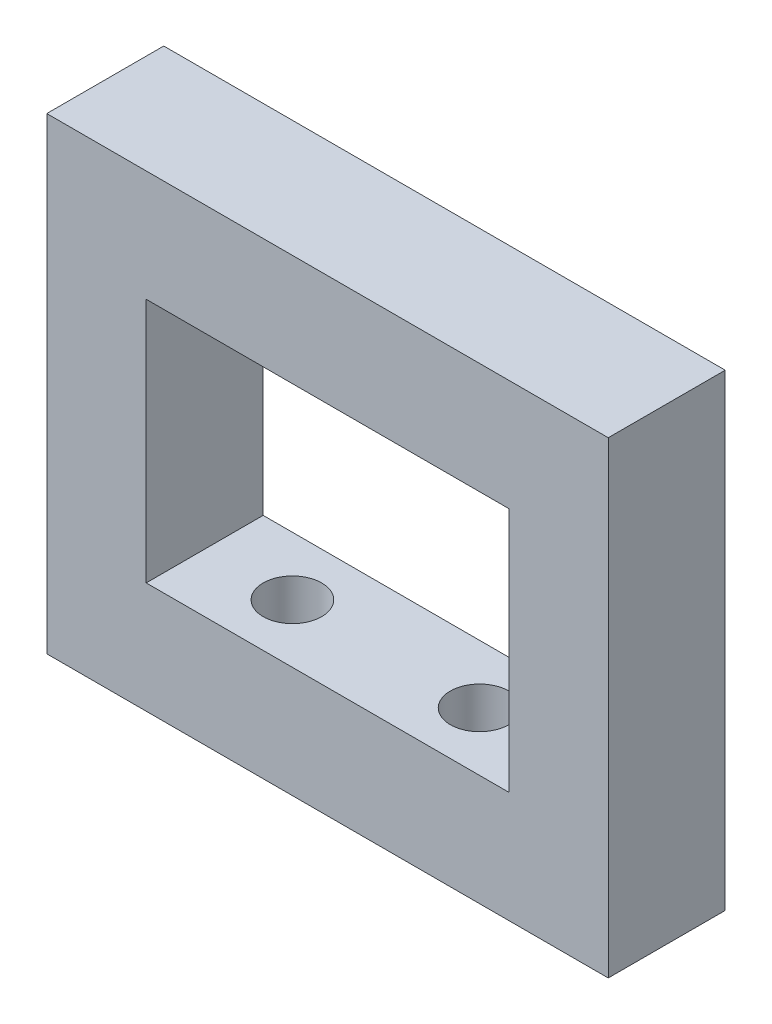
SolidWorks part; units mm, degrees
material "ABS"
ref_plane "前基準面" through (0, 0, 0) normal (0, 0, 1) x (1, 0, 0)
ref_plane "上基準面" through (0, 0, 0) normal (0, 1, 0) x (1, 0, 0)
ref_plane "右基準面" through (0, 0, 0) normal (1, 0, 0) x (0, 0, -1)
sketch "草圖1" plane through (0, 0, 0) normal (0, 0, 1) x (1, 0, 0)
  line L1 (-12, -10) -> (12, -10)
  line L2 (-12, -10) -> (-12, 10)
  line L3 (-12, 10) -> (12, 10)
  line L4 (12, -10) -> (12, 10)
  line L5 (-12, -10) -> (12, 10) construction
  line L6 (-12, 10) -> (12, -10) construction
  point P0 (0, 0)
  dimension "D1" = 24
  dimension "D2" = 20
extrude "填料-伸長1" add sketch "草圖1" along normal mid plane 5
sketch "草圖2" plane through (0, 0, 2.5) normal (0, 0, 1) x (1, 0, 0)
  line L1 (-7.75, -5.25) -> (7.75, -5.25)
  line L2 (-7.75, -5.25) -> (-7.75, 5.25)
  line L3 (-7.75, 5.25) -> (7.75, 5.25)
  line L4 (7.75, -5.25) -> (7.75, 5.25)
  line L5 (-7.75, -5.25) -> (7.75, 5.25) construction
  line L6 (-7.75, 5.25) -> (7.75, -5.25) construction
  point P0 (0, 0)
  dimension "D1" = 15.5
  dimension "D2" = 10.5
extrude "除料-伸長1" cut sketch "草圖2" against normal through all
sketch "草圖4" plane through (0, -10, 0) normal (0, -1, 0) x (1, 0, 0)
  line L0 (-4, 0) -> (4, 0) construction
  circle A0 centre (-4, 0) radius 1.25
  circle A1 centre (4, 0) radius 1.25
  point P3 (0, 0)
  dimension "D1" = 2.5
  dimension "D2" = 8
extrude "除料-伸長2" cut sketch "草圖4" against normal up to next
